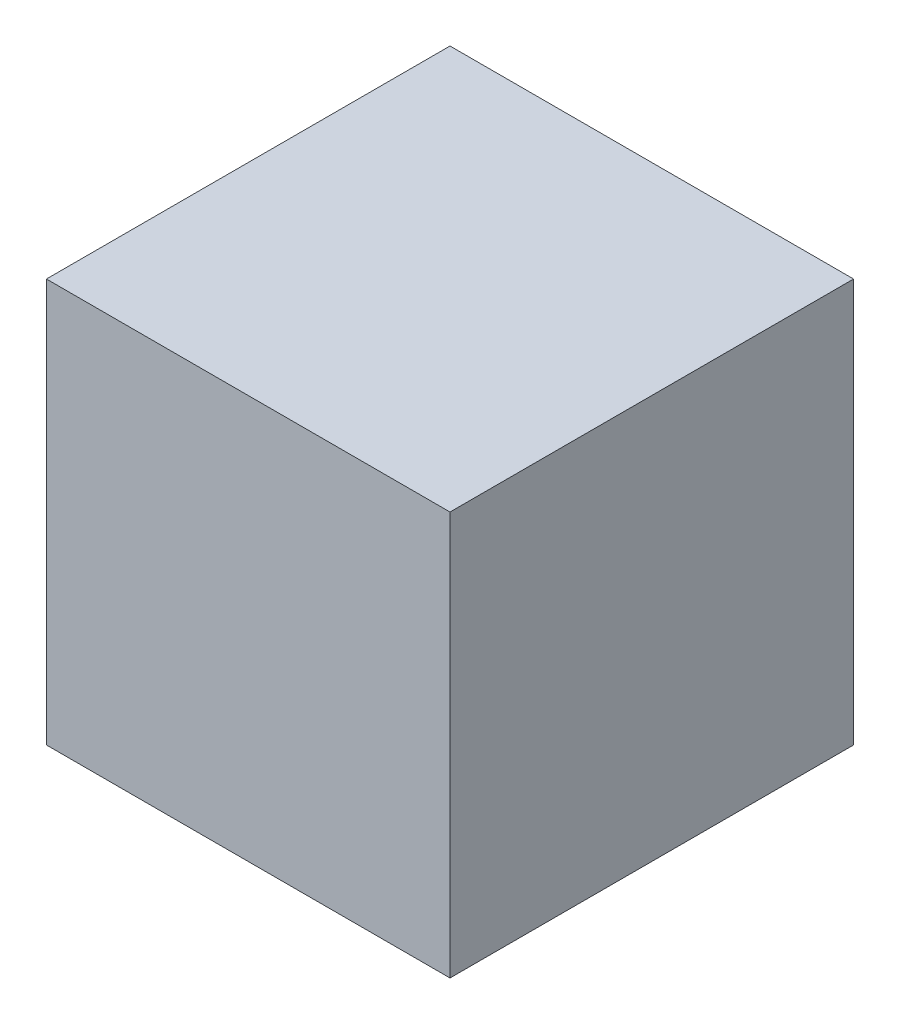
SolidWorks part; units mm, degrees
ref_plane "Front Plane" through (0, 0, 0) normal (0, 0, 1) x (1, 0, 0)
ref_plane "Top Plane" through (0, 0, 0) normal (0, 1, 0) x (1, 0, 0)
ref_plane "Right Plane" through (0, 0, 0) normal (1, 0, 0) x (0, 0, -1)
sketch "Sketch1" plane through (0, 0, 0) normal (0, 0, 1) x (1, 0, 0)
  line L1 (0, 0) -> (-50, 0)
  line L2 (0, 0) -> (0, 50)
  line L3 (0, 50) -> (-50, 50)
  line L4 (-50, 0) -> (-50, 50)
  dimension "D1" = 50
  dimension "D2" = 50
extrude "Boss-Extrude1" add sketch "Sketch1" along normal blind 50
